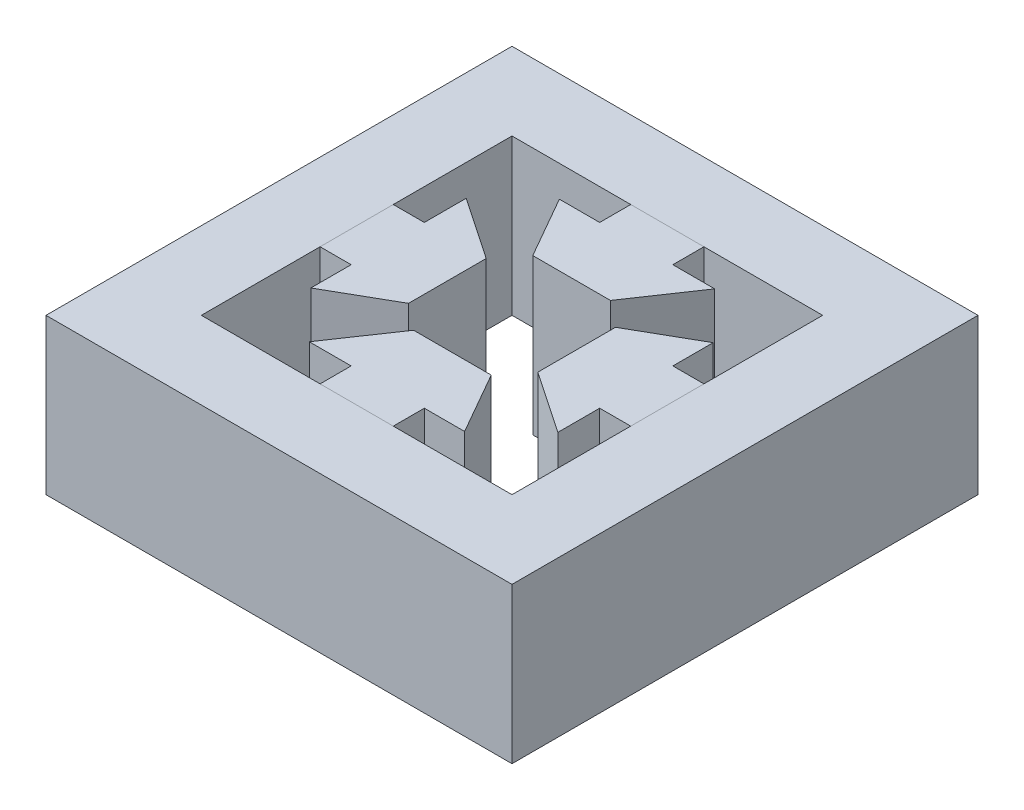
SolidWorks part; units mm, degrees
ref_plane "Front Plane" through (0, 0, 0) normal (0, 0, 1) x (1, 0, 0)
ref_plane "Top Plane" through (0, 0, 0) normal (0, 1, 0) x (1, 0, 0)
ref_plane "Right Plane" through (0, 0, 0) normal (1, 0, 0) x (0, 0, -1)
sketch "Sketch1" plane through (0, 0, 0) normal (0, 1, 0) x (1, 0, 0)
  line L0 (-15, -15) -> (-15, 15)
  line L1 (10, -10) -> (-10, -10)
  line L2 (10, -10) -> (10, 10)
  line L3 (10, 10) -> (-10, 10)
  line L4 (-10, -10) -> (-10, 10)
  line L5 (10, -10) -> (-10, 10) construction
  line L6 (10, 10) -> (-10, -10) construction
  line L7 (15, 15) -> (-15, 15)
  line L8 (15, -15) -> (15, 15)
  line L9 (15, -15) -> (-15, -15)
  point P0 (0, 0)
  dimension "D1" = 20
  dimension "D2" = 20
  dimension "D3" = 5
extrude "Boss-Extrude1" add sketch "Sketch1" along normal blind 10
sketch "Sketch2" plane through (0, 10, 0) normal (0, 1, 0) x (1, 0, 0)
  line L0 (4, -2.3365) -> (4, 2.6635)
  line L1 (8, -2.3555) -> (8, 2.3555)
  line L2 (8, -5.0498) -> (8, 4.9502)
  line L3 (10, -10) -> (10, 10) construction
  line L4 (4, 2.6635) -> (8, 4.9502)
  line L5 (4, -2.3365) -> (8, -5.0498)
  line L6 (8, -2.3555) -> (10, -2.3555)
  line L7 (8, 2.3555) -> (10, 2.3555)
  line L8 (10, 2.3555) -> (10, -2.3555)
  line L9 (-2.3365, -4) -> (-5.0498, -8)
  line L10 (-5.0498, -8) -> (4.9502, -8)
  line L11 (2.6635, -4) -> (4.9502, -8)
  line L12 (-2.3365, -4) -> (2.6635, -4)
  line L13 (2.3555, -10) -> (-2.3555, -10)
  line L14 (-2.3555, -8) -> (-2.3555, -10)
  line L15 (-2.3555, -8) -> (2.3555, -8)
  line L16 (2.3555, -8) -> (2.3555, -10)
  line L17 (-4, 2.3365) -> (-8, 5.0498)
  line L18 (-8, 5.0498) -> (-8, -4.9502)
  line L19 (-4, -2.6635) -> (-8, -4.9502)
  line L20 (-4, 2.3365) -> (-4, -2.6635)
  line L21 (-10, -2.3555) -> (-10, 2.3555)
  line L22 (-8, 2.3555) -> (-10, 2.3555)
  line L23 (-8, 2.3555) -> (-8, -2.3555)
  line L24 (-8, -2.3555) -> (-10, -2.3555)
  line L25 (2.3365, 4) -> (5.0498, 8)
  line L26 (5.0498, 8) -> (-4.9502, 8)
  line L27 (-2.6635, 4) -> (-4.9502, 8)
  line L28 (2.3365, 4) -> (-2.6635, 4)
  line L29 (-2.3555, 10) -> (2.3555, 10)
  line L30 (2.3555, 8) -> (2.3555, 10)
  line L31 (2.3555, 8) -> (-2.3555, 8)
  line L32 (-2.3555, 8) -> (-2.3555, 10)
  point P3 (4, 0.1635)
  point P6 (8, 0)
  point P9 (8, -0.0498)
  point P40 (0, 0)
  line M9 (-10, 10) -> (10, 10)
  line M10 (10, 10) -> (10, -10)
  line M11 (10, -10) -> (-10, -10)
  dimension "D1" = 2
  dimension "D2" = 10
  dimension "D3" = 5
  dimension "D4" = 0
  dimension "D5" = 4
  dimension "D6" = 4
extrude "Boss-Extrude2" add sketch "Sketch2" against normal blind 10 separate body contours L28 L25 L26 L27 | L32 L26 L30 M9 | L20 L17 L18 L19 | L12 L9 L10 L11 | L16 L10 L14 M11 | L0 L5 L2 L1 L4 | L7 L1 L6 M10 | L21 L22 L23 L24
